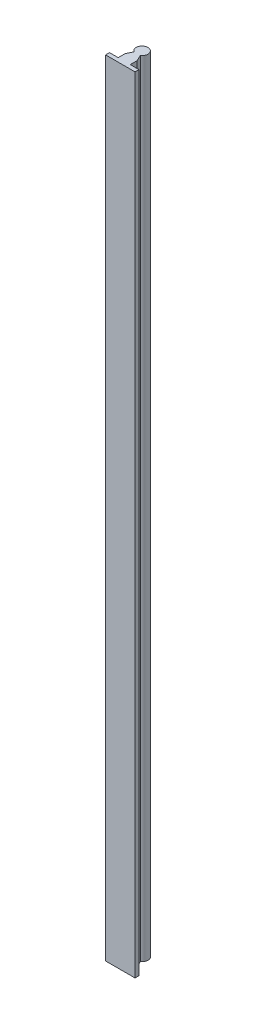
SolidWorks part; units mm, degrees
ref_plane "Front Plane" through (0, 0, 0) normal (0, 0, 1) x (1, 0, 0)
ref_plane "Top Plane" through (0, 0, 0) normal (0, 1, 0) x (1, 0, 0)
ref_plane "Right Plane" through (0, 0, 0) normal (1, 0, 0) x (0, 0, -1)
sketch "Sketch1" plane through (0, 0, 0) normal (0, 1, 0) x (1, 0, 0)
  line L0 (0, 18.009) -> (0, -22.7347) construction
  line L1 (-3.25, -5.0436) -> (-6.15, -11.2)
  line L7 (3.25, -5.0436) -> (6.15, -11.2)
  line L8 (-6.15, -11.2) -> (-6.15, -18.2)
  line L9 (-6.15, -18.2) -> (-15, -18.2)
  line L10 (-15, -18.2) -> (-15, -22.2)
  line L11 (-15, -22.2) -> (15, -22.2)
  line L12 (15, -18.2) -> (15, -22.2)
  line L13 (6.15, -18.2) -> (15, -18.2)
  line L14 (6.15, -11.2) -> (6.15, -18.2)
  arc A0 (3.25, -5.0436) -> (-3.25, -5.0436) centre (0, 0) ccw
  point P11 (0, -22.2)
  point P12 (0, -9.655)
  point P16 (0, 6)
  dimension "D1" = 12
  dimension "D2" = 30
  dimension "D3" = 4
  dimension "D4" = 28.2
  dimension "D5" = 12.3
  dimension "D6" = 7
  dimension "D7" = 6.5
extrude "Boss-Extrude1" add sketch "Sketch1" along normal blind 800
